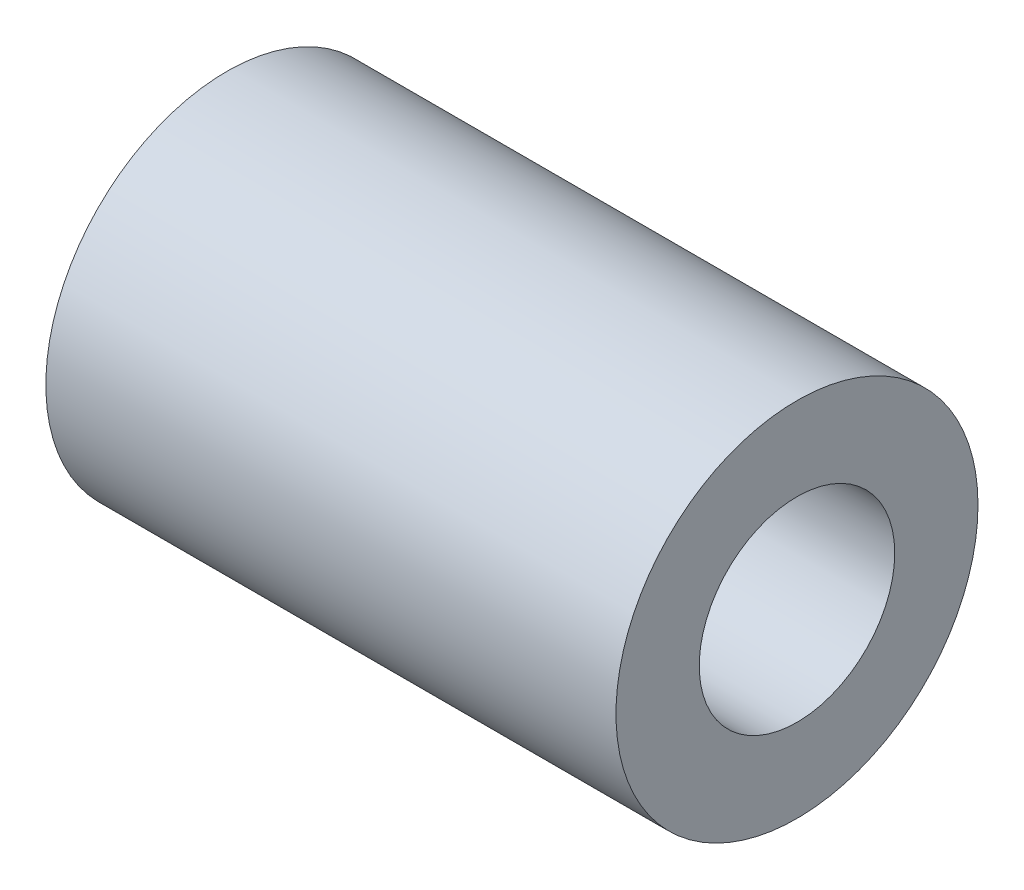
SolidWorks part; units mm, degrees
ref_plane "Plan de face" through (0, 0, 0) normal (0, 0, 1) x (1, 0, 0)
ref_plane "Plan de dessus" through (0, 0, 0) normal (0, 1, 0) x (1, 0, 0)
ref_plane "Plan de droite" through (0, 0, 0) normal (1, 0, 0) x (0, 0, -1)
sketch "Esquisse1" plane through (0, 0, 0) normal (1, 0, 0) x (0, 0, -1)
  circle A0 centre (0, 0) radius 3.429
  circle A1 centre (0, 0) radius 6.35
  dimension "D1" = 6.858
  dimension "D2" = 12.7
extrude "Boss.-Extru.1" add sketch "Esquisse1" against normal blind 20
equation "\"D1@Boss.-Extru.1\"=20mm"
